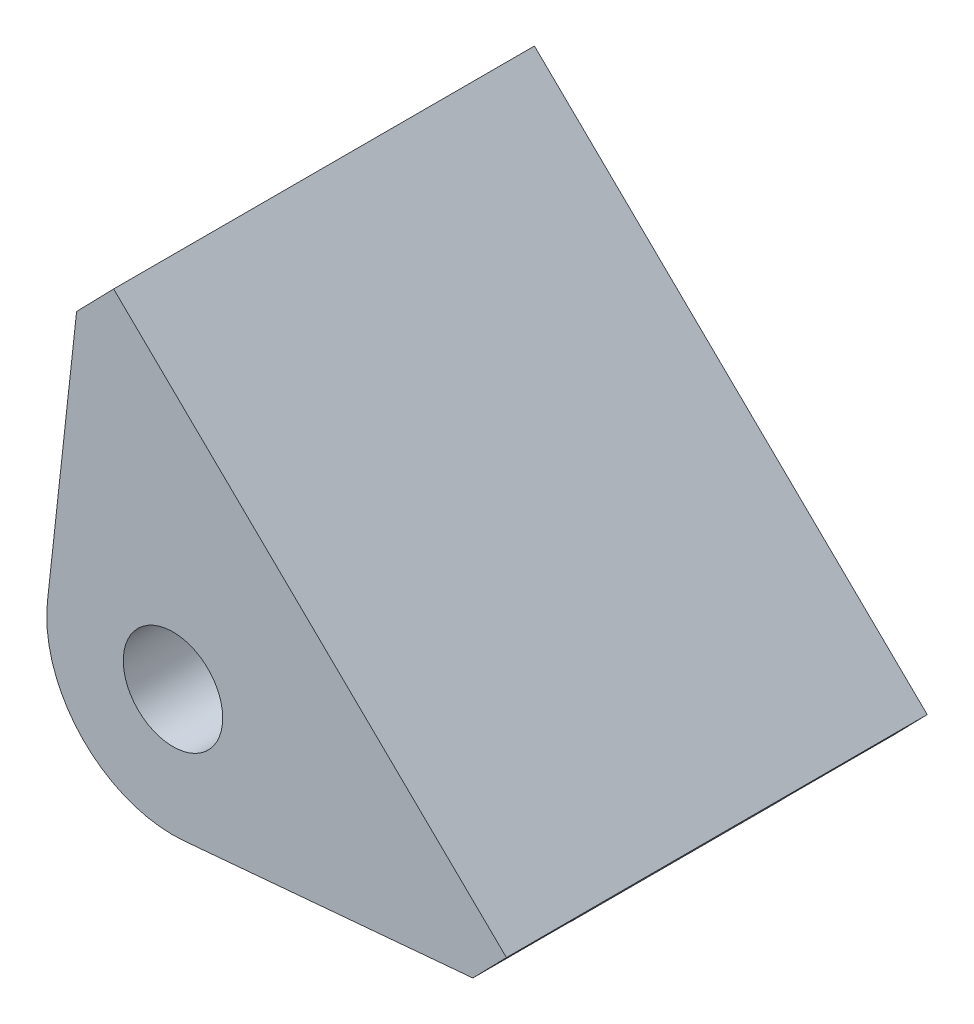
SolidWorks part; units mm, degrees
ref_plane "Front Plane" through (0, 0, 0) normal (0, 0, 1) x (1, 0, 0)
ref_plane "Top Plane" through (0, 0, 0) normal (0, 1, 0) x (1, 0, 0)
ref_plane "Right Plane" through (0, 0, 0) normal (1, 0, 0) x (0, 0, -1)
sketch "Sketch1" plane through (0, 0, 0) normal (0, 0, 1) x (1, 0, 0)
  line L0 (-1425.6478, 709.2798) -> (-1430.0493, 669.1822)
  line L1 (-1371.0638, 656.11) -> (-1425.6478, 709.2798)
  line L2 (-1425.6478, 709.2798) -> (-1371.0638, 656.11)
  line L3 (-1425.6478, 709.2798) -> (-1451.9221, 682.3066)
  line L4 (-1371.0638, 656.11) -> (-1397.338, 629.1369)
  line L5 (-1451.9221, 682.3066) -> (-1397.338, 629.1369)
  line L6 (-1425.6478, 709.2798) -> (-1397.338, 629.1369) construction
  line L7 (-1371.0638, 656.11) -> (-1451.9221, 682.3066) construction
  line L8 (-1413.553, 652.339) -> (-1371.0638, 656.11)
  arc A0 (-1430.0493, 669.1822) -> (-1413.553, 652.339) centre (-1414.9003, 667.5193) ccw
  circle A3 centre (-1414.9003, 667.5193) radius 6.0007
  circle A4 centre (-1414.9003, 667.5193) radius 15.24
  point P10 (-1411.4929, 669.2083)
extrude "Boss-Extrude1" add sketch "Sketch1" along normal blind 12.7 contours L0 A0 L8 L1 A3 | A0 A4 A3
ref_plane "Plane1" through (0, 0, -12.7) normal (0, 0, -1) x (-1, 0, 0)
sketch "Sketch2" plane through (0, 0, -12.7) normal (0, 0, -1) x (-1, 0, 0)
  line L1 (1371.0638, 656.11) -> (1425.6478, 709.2798)
  line L5 (1379.6518, 654.4593) -> (1427.0726, 700.6514)
  line L6 (1371.0638, 656.11) -> (1374.6454, 659.5988) construction
  line L7 (1374.6454, 659.5988) -> (1379.6518, 654.4593) construction
  line L8 (1425.6478, 709.2798) -> (1430.6542, 704.1403) construction
  line L9 (1430.6542, 704.1403) -> (1427.0726, 700.6514) construction
  line L10 (1427.0726, 700.6514) -> (1430.6542, 704.1403)
  line L11 (1427.0726, 700.6514) -> (1422.0662, 705.7909)
  line L12 (1430.6542, 704.1403) -> (1425.6478, 709.2798)
  line L13 (1422.0662, 705.7909) -> (1425.6478, 709.2798)
  line L14 (1427.0726, 700.6514) -> (1425.6478, 709.2798) construction
  line L15 (1430.6542, 704.1403) -> (1422.0662, 705.7909) construction
  line L16 (1379.6518, 654.4593) -> (1427.0726, 700.6514)
  line L17 (1379.6518, 654.4593) -> (1374.6454, 659.5988)
  line L18 (1427.0726, 700.6514) -> (1422.0662, 705.7909)
  line L19 (1374.6454, 659.5988) -> (1422.0662, 705.7909)
  line L20 (1379.6518, 654.4593) -> (1422.0662, 705.7909) construction
  line L21 (1427.0726, 700.6514) -> (1374.6454, 659.5988) construction
  line L22 (1379.6518, 654.4593) -> (1374.6454, 659.5988)
  line L23 (1379.6518, 654.4593) -> (1376.0701, 650.9705)
  line L24 (1374.6454, 659.5988) -> (1371.0638, 656.11)
  line L25 (1376.0701, 650.9705) -> (1371.0638, 656.11)
  line L26 (1379.6518, 654.4593) -> (1371.0638, 656.11) construction
  line L27 (1374.6454, 659.5988) -> (1376.0701, 650.9705) construction
  circle A1 centre (1414.9003, 667.5193) radius 15.24
  point P11 (1426.3602, 704.9656)
  point P14 (1400.859, 680.1251)
  point P16 (1375.3578, 655.2847)
  dimension "D1" = 66.2
  dimension "D2" = 5
  dimension "D3" = 5
extrude "Boss-Extrude2" add sketch "Sketch2" along normal mid plane 25.4 contours L17 L5 L16 L11 L1
mirror "Mirror2" about plane through (0, 0, -12.7) normal (0, 0, -1) of "Boss-Extrude1"
sketch "Sketch4" plane through (0, 0, -12.7) normal (0, 0, -1) x (-1, 0, 0)
  line L0 (1422.0662, 705.7909) -> (1425.6478, 709.2798) construction
  line L1 (1426.6411, 700.2311) -> (1427.0726, 700.6514) construction
  line L2 (1422.0662, 705.7909) -> (1425.6478, 709.2798) construction
  line L3 (1426.6411, 700.2311) -> (1427.0726, 700.6514)
  line L4 (1427.0726, 700.6514) -> (1422.0662, 705.7909)
  line L5 (1427.0726, 700.6514) -> (1430.6542, 704.1403)
  line L6 (1422.0662, 705.7909) -> (1425.6478, 709.2798)
  line L7 (1430.6542, 704.1403) -> (1425.6478, 709.2798)
  line L8 (1427.0726, 700.6514) -> (1425.6478, 709.2798) construction
  line L9 (1422.0662, 705.7909) -> (1430.6542, 704.1403) construction
  line L10 (1371.0638, 656.11) -> (1374.6454, 659.5988) construction
  line L11 (1379.6518, 654.4593) -> (1380.4877, 655.2736) construction
  line L12 (1371.0638, 656.11) -> (1374.6454, 659.5988)
  line L13 (1379.6518, 654.4593) -> (1380.4877, 655.2736)
  line L14 (1379.6518, 654.4593) -> (1374.6454, 659.5988)
  line L15 (1379.6518, 654.4593) -> (1376.0701, 650.9705)
  line L16 (1374.6454, 659.5988) -> (1371.0638, 656.11)
  line L17 (1376.0701, 650.9705) -> (1371.0638, 656.11)
  line L18 (1379.6518, 654.4593) -> (1371.0638, 656.11) construction
  line L19 (1374.6454, 659.5988) -> (1376.0701, 650.9705) construction
  point P7 (1426.3602, 704.9656)
  point P12 (1375.3578, 655.2847)
extrude "Cut-Extrude1" cut sketch "Sketch4" against normal through all both and the other way through all contours L17 L15 L14 L12 | L5 L7 L6 L4
equation "\"D1@Boss-Extrude1\"=1in/2"
